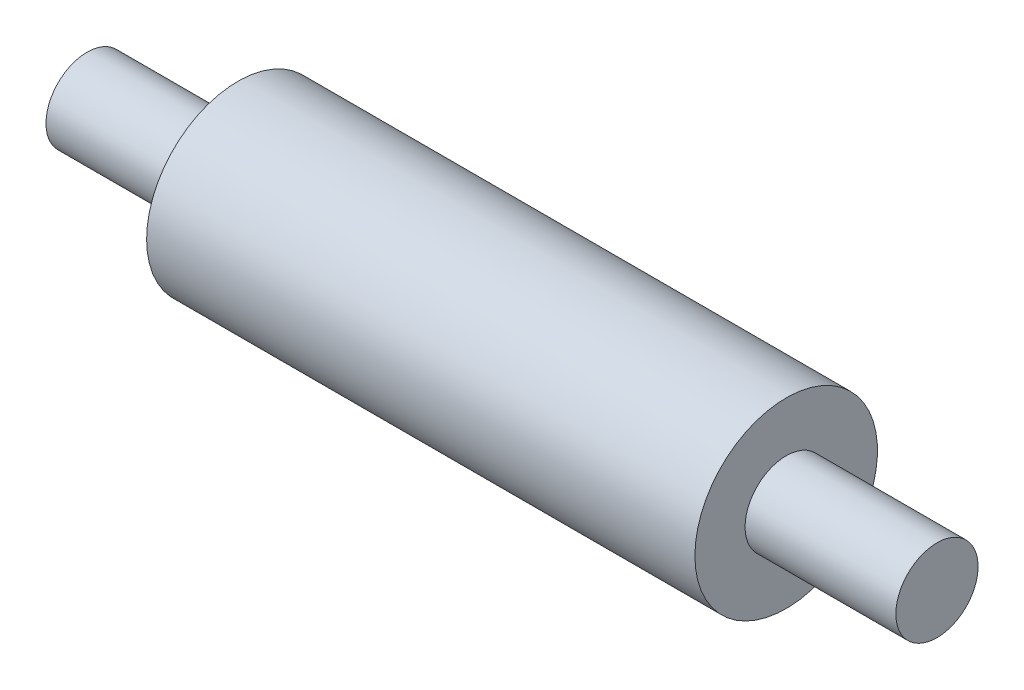
SolidWorks part; units mm, degrees
material "Brass"
ref_plane "Front Plane" through (0, 0, 0) normal (0, 0, 1) x (1, 0, 0)
ref_plane "Top Plane" through (0, 0, 0) normal (0, 1, 0) x (1, 0, 0)
ref_plane "Right Plane" through (0, 0, 0) normal (1, 0, 0) x (0, 0, -1)
sketch "Sketch1" plane through (0, 0, 0) normal (0, 0, 1) x (1, 0, 0)
  line L0 (10, -1.5) -> (15.5, -1.5)
  line L1 (-15.5, 1.5) -> (-10, 1.5)
  line L2 (-15.5, 1.5) -> (-15.5, -1.5)
  line L3 (-15.5, -1.5) -> (-10, -1.5)
  line L4 (15.5, 1.5) -> (15.5, -1.5)
  line L5 (-15.5, 1.5) -> (15.5, -1.5) construction
  line L6 (-15.5, -1.5) -> (15.5, 1.5) construction
  line L7 (-10, 3.33) -> (10, 3.33)
  line L8 (-10, 3.33) -> (-10, -3.33)
  line L9 (-10, -3.33) -> (10, -3.33)
  line L10 (10, 3.33) -> (10, -3.33)
  line L11 (-10, 3.33) -> (10, -3.33) construction
  line L12 (-10, -3.33) -> (10, 3.33) construction
  line L13 (10, 1.5) -> (15.5, 1.5)
  line L14 (-15.5, 0) -> (15.5, 0)
  point P0 (0, 0)
  point P6 (0, 0)
  dimension "D1" = 31
  dimension "D2" = 3
  dimension "D3" = 6.66
  dimension "D4" = 20
revolve "Revolve1" add sketch "Sketch1" angle 360 about L14
